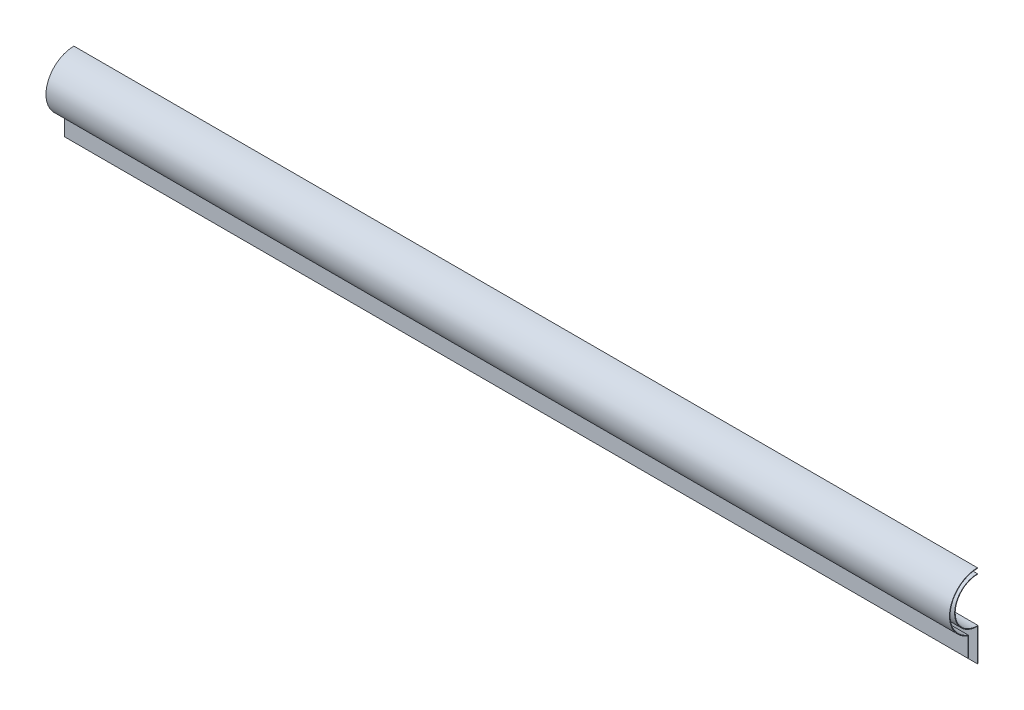
SolidWorks part; units mm, degrees
material "Thornel Mat VMA"
ref_plane "Płaszczyzna XY" through (0, 0, 0) normal (0, 0, 1) x (1, 0, 0)
ref_plane "Płaszczyzna XZ" through (0, 0, 0) normal (0, 1, 0) x (1, 0, 0)
ref_plane "Płaszczyzna YZ" through (0, 0, 0) normal (1, 0, 0) x (0, 0, -1)
sketch "Szkic1" plane through (-26.203, 0, 0) normal (1, 0, 0) x (0, 0, -1)
  line L0 (-237.6816, 742.5) -> (-237.6816, 745) construction
  line L1 (-237.6816, 717.5) -> (-237.6816, 700) construction
  line L2 (-242.6816, 705) -> (-242.6816, 715.8579) construction
  line L3 (-237.6816, 742.5) -> (-237.6816, 745)
  line L4 (-237.6816, 717.5) -> (-237.6816, 700)
  line L5 (-242.6816, 705) -> (-242.6816, 715.8579)
  line L6 (-242.6816, 705) -> (-237.6816, 700)
  arc A0 (-237.6816, 742.5) -> (-237.6816, 717.5) centre (-237.6816, 730) ccw construction
  arc A1 (-237.6816, 745) -> (-242.6816, 715.8579) centre (-237.6816, 730) ccw construction
  arc A2 (-237.6816, 742.5) -> (-237.6816, 717.5) centre (-237.6816, 730) ccw
  arc A3 (-237.6816, 745) -> (-242.6816, 715.8579) centre (-237.6816, 730) ccw
extrude "Dodanie-wyciągnięcie1" add sketch "Szkic1" against normal up to surface (495 mm away)
shell "Skorupa1" thickness 0.3
sketch "Szkic2" plane through (-521.203, 0, 0) normal (-1, 0, 0) x (0, 0, 1)
  line L0 (242.6816, 705) -> (237.6816, 705)
  line L1 (237.6816, 717.5) -> (237.6816, 700) construction
  line L2 (237.6816, 705) -> (237.6816, 695.3832)
  line L3 (237.6816, 695.3832) -> (244.8976, 695.3832)
  line L4 (244.8976, 695.3832) -> (244.8976, 705)
  line L5 (244.8976, 705) -> (242.6816, 705)
  line L6 (237.6816, 746.7125) -> (237.6816, 741.2795)
  line L7 (237.6816, 741.2795) -> (237.1442, 741.2795)
  line L8 (237.1442, 741.2795) -> (237.1442, 746.7125)
  line L9 (237.1442, 746.7125) -> (237.6816, 746.7125)
extrude "Wytnij-wyciągnięcie1" cut sketch "Szkic2" against normal through all
sketch "Szkic3" plane through (-26.203, 0, 0) normal (1, 0, 0) x (0, 0, -1)
  line L0 (-237.6816, 699.7) -> (-237.1315, 699.7)
  line L1 (-237.1315, 699.7) -> (-237.1315, 698.976)
  line L2 (-237.1315, 698.976) -> (-237.9773, 698.976)
  line L3 (-237.9773, 698.976) -> (-237.6816, 699.7)
extrude "Wytnij-wyciągnięcie2" cut sketch "Szkic3" against normal through all
